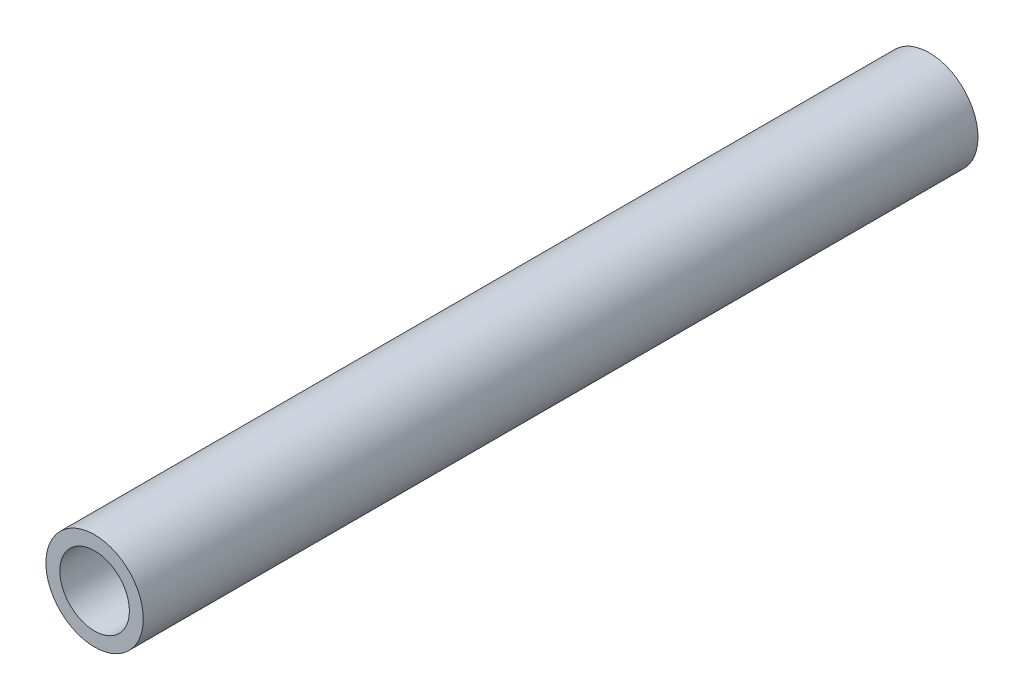
SolidWorks part; units mm, degrees
ref_plane "Front Plane" through (0, 0, 0) normal (0, 0, 1) x (1, 0, 0)
ref_plane "Top Plane" through (0, 0, 0) normal (0, 1, 0) x (1, 0, 0)
ref_plane "Right Plane" through (0, 0, 0) normal (1, 0, 0) x (0, 0, -1)
sketch "Sketch1" plane through (0, 0, 0) normal (0, 0, 1) x (1, 0, 0)
  circle A0 centre (0, 0) radius 9.525
  circle A1 centre (0, 0) radius 13.335
  dimension "D1" = 19.05
  dimension "D2" = 26.67
extrude "Boss-Extrude1" add sketch "Sketch1" along normal blind 228.6
